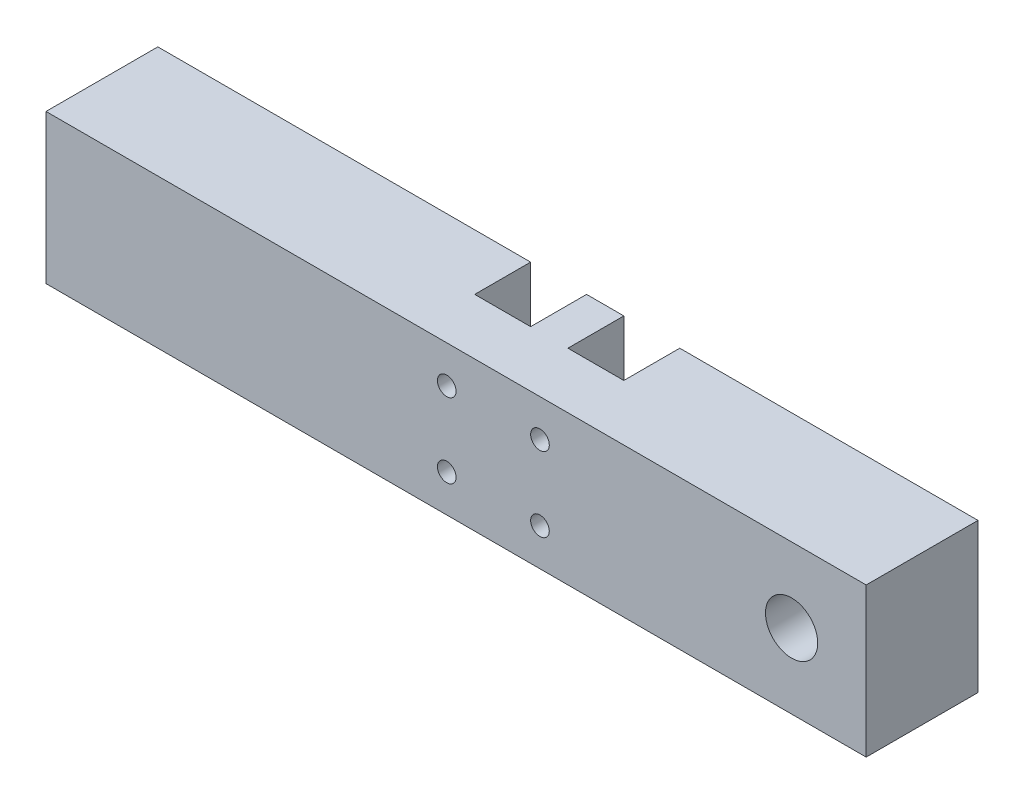
SolidWorks part; units mm, degrees
ref_plane "Front Plane" through (0, 0, 0) normal (0, 0, 1) x (1, 0, 0)
ref_plane "Top Plane" through (0, 0, 0) normal (0, 1, 0) x (1, 0, 0)
ref_plane "Right Plane" through (0, 0, 0) normal (1, 0, 0) x (0, 0, -1)
sketch "Sketch1" plane through (0, 0, 0) normal (0, 0, 1) x (1, 0, 0)
  line L1 (-110, 20) -> (110, 20)
  line L2 (-110, 20) -> (-110, -20)
  line L3 (-110, -20) -> (110, -20)
  line L4 (110, 20) -> (110, -20)
  line L5 (-110, 20) -> (110, -20) construction
  line L6 (-110, -20) -> (110, 20) construction
  point P0 (0, 0)
  dimension "D1" = 220
  dimension "D2" = 40
extrude "Boss-Extrude1" add sketch "Sketch1" along normal blind 30
sketch "Sketch2" plane through (0, 0, 0) normal (0, 0, 1) x (1, 0, 0)
  line L0 (-110, 20) -> (-110, -20) construction
  circle A0 centre (90, 0) radius 10
  dimension "D1" = 200
extrude "Cut-Extrude1" cut sketch "Sketch2" along normal blind 7
sketch "Sketch3" plane through (0, 0, 0) normal (0, 0, -1) x (-1, 0, 0)
  circle A0 centre (-90, 0) radius 7
extrude "Cut-Extrude2" cut sketch "Sketch3" against normal up to vertex
sketch "Sketch4" plane through (0, 0, 0) normal (0, 0, -1) x (-1, 0, 0)
  line L0 (-110, 20) -> (110, 20) construction
  line L1 (-30, 20) -> (-15, 20)
  line L2 (-30, 20) -> (-30, -20)
  line L3 (-30, -20) -> (-15, -20)
  line L4 (-15, 20) -> (-15, -20)
  line L5 (110, -20) -> (-110, -20) construction
  line L6 (-110, -20) -> (-110, 20) construction
  line L7 (-10, 20) -> (-10, -20) construction
  line L8 (-5, 20) -> (-5, -20)
  line L9 (10, -20) -> (-5, -20)
  line L10 (10, 20) -> (10, -20)
  line L11 (10, 20) -> (-5, 20)
  dimension "D1" = 80
  dimension "D2" = 15
  dimension "D3" = 10
extrude "Cut-Extrude3" cut sketch "Sketch4" against normal blind 15
sketch "Sketch5" plane through (0, 0, 0) normal (0, 0, -1) x (-1, 0, 0)
  line L0 (-30, 20) -> (-30, -20) construction
  line L1 (-15, 20) -> (-30, 20) construction
  line L2 (-90, 0) -> (0, 0) construction
  line L3 (-10, 20) -> (-10, -20) construction
  line L4 (-15, 20) -> (-5, 20) construction
  line L5 (-5, -20) -> (-15, -20) construction
  circle A0 centre (-22.5, 10) radius 2.5
  circle A1 centre (-22.5, -10) radius 2.5
  circle A2 centre (2.5, -10) radius 2.5
  circle A3 centre (2.5, 10) radius 2.5
  dimension "D1" = 7.5
  dimension "D2" = 10
extrude "Cut-Extrude4" cut sketch "Sketch5" against normal up to vertex
